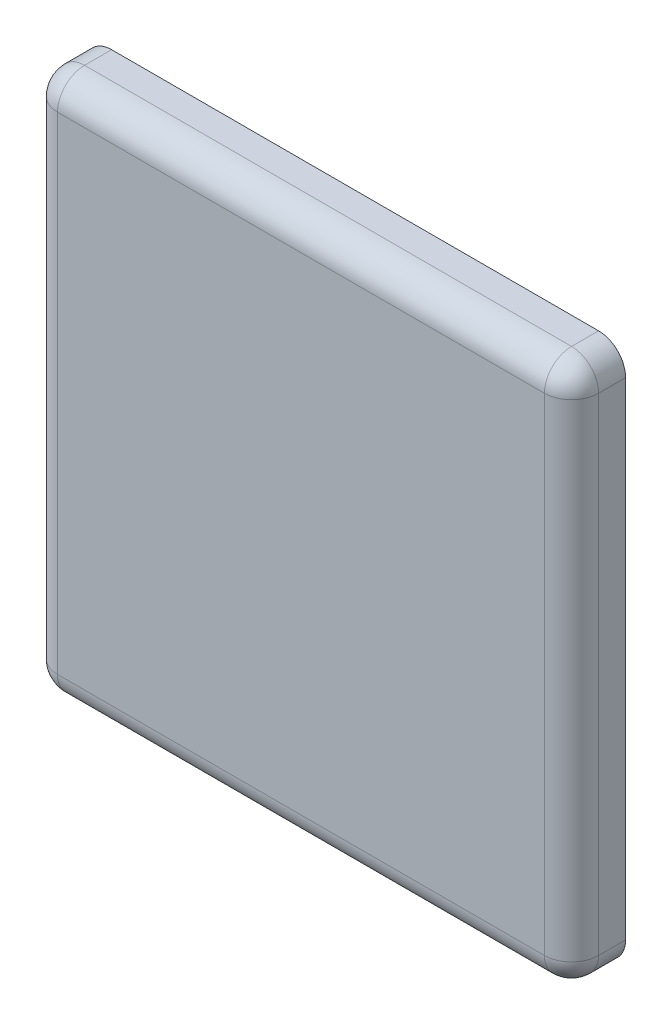
SolidWorks part; units mm, degrees
ref_plane "Front Plane" through (0, 0, 0) normal (0, 0, 1) x (1, 0, 0)
ref_plane "Top Plane" through (0, 0, 0) normal (0, 1, 0) x (1, 0, 0)
ref_plane "Right Plane" through (0, 0, 0) normal (1, 0, 0) x (0, 0, -1)
sketch "Sketch1" plane through (0, 0, 0) normal (0, 0, 1) x (1, 0, 0)
  line L1 (0, 0) -> (20, 0)
  line L2 (0, 0) -> (0, 20)
  line L3 (0, 20) -> (20, 20)
  line L4 (20, 0) -> (20, 20)
  dimension "D1" = 20
  dimension "D2" = 20
extrude "Extrude1" add sketch "Sketch1" along normal blind 2
fillet "Fillet1" radius 1 8 edges at (20, 10, 2) (10, 0, 2) (0, 10, 2) (10, 20, 2) (20, 0, 1) (0, 0, 1) (0, 20, 1) (20, 20, 1)
